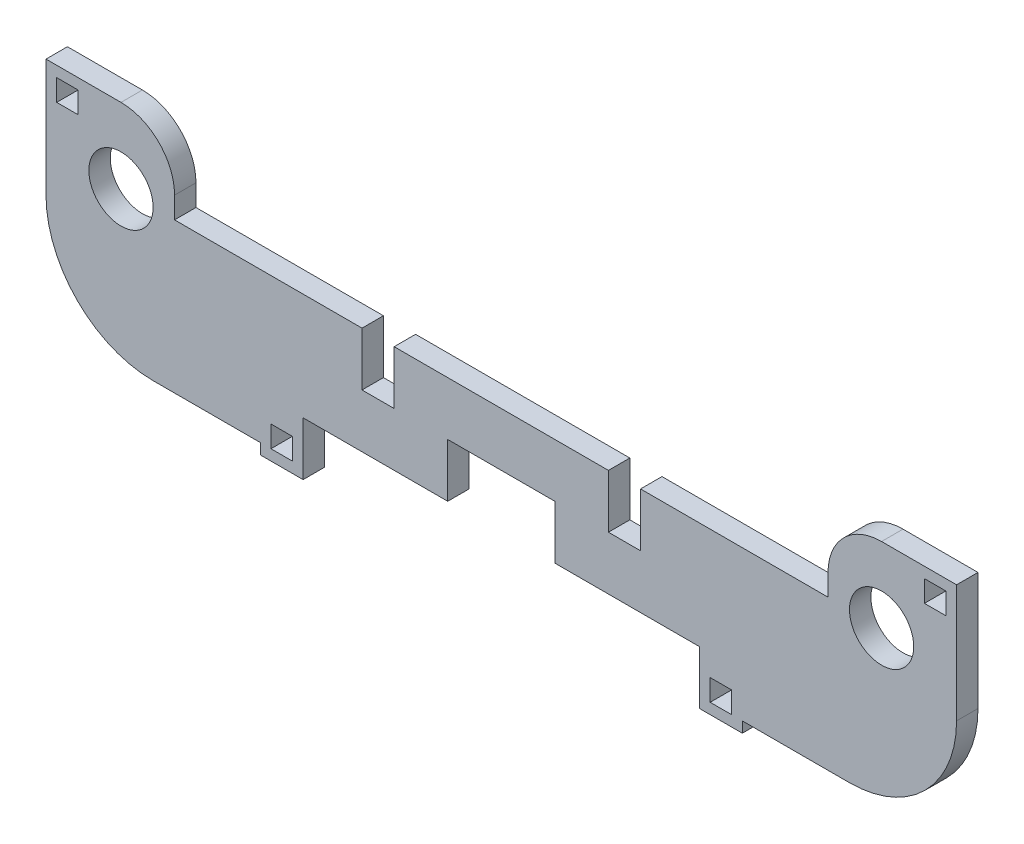
SolidWorks part; units mm, degrees
ref_plane "Front Plane" through (0, 0, 0) normal (0, 0, 1) x (1, 0, 0)
ref_plane "Top Plane" through (0, 0, 0) normal (0, 1, 0) x (1, 0, 0)
ref_plane "Right Plane" through (0, 0, 0) normal (1, 0, 0) x (0, 0, -1)
sketch "Sketch1" plane through (0, 0, 0) normal (0, 0, 1) x (1, 0, 0)
  line L0 (-35.5, -5) -> (35.5, 5) construction
  line L1 (-35.5, -5) -> (35.5, -5)
  line L2 (-35.5, -5) -> (-35.5, 5)
  line L3 (-35.5, 5) -> (-13, 5)
  line L4 (35.5, -5) -> (35.5, 5)
  line L5 (35.5, -5) -> (0, 0) construction
  line L6 (0, 0) -> (-35.5, 5) construction
  line L7 (-13, 5) -> (-13, 0)
  line L8 (-13, 0) -> (13, 0)
  line L9 (13, 0) -> (13, 5)
  line L10 (13, 5) -> (35.5, 5)
  line L11 (0, 0) -> (0, -5) construction
  line L12 (-35.5, 0) -> (-42.5, 0)
  line L13 (-42.5, 0) -> (-42.5, 12)
  line L14 (-42.5, 12) -> (-30.5, 12)
  line L15 (-30.5, 12) -> (-30.5, 5)
  line L16 (35.5, 0) -> (42.5, 0)
  line L17 (-41.5, 9) -> (-39.5, 9)
  line L18 (-41.5, 9) -> (-41.5, 11)
  line L19 (-41.5, 11) -> (-39.5, 11)
  line L20 (-39.5, 9) -> (-39.5, 11)
  line L21 (42.5, 0) -> (42.5, 12)
  line L22 (41.5, 11) -> (39.5, 11)
  line L23 (41.5, 9) -> (41.5, 11)
  line L24 (41.5, 9) -> (39.5, 9)
  line L25 (39.5, 9) -> (39.5, 11)
  line L26 (30.5, 12) -> (30.5, 5)
  line L27 (42.5, 12) -> (30.5, 12)
  line L28 (-5, -5) -> (-5, 0)
  line L29 (-5, 0) -> (5, 0)
  line L30 (5, 0) -> (5, -5)
  line L31 (0, 0) -> (0, -5) construction
  line L32 (-10, 0) -> (-10, 5)
  line L33 (-10, 5) -> (10, 5)
  line L34 (10, 5) -> (10, 0)
  line L35 (10, 0) -> (-10, 0)
  line L36 (0, 5) -> (0, 0) construction
  line L37 (18.5, -9) -> (18.5, -5)
  line L38 (-18.5, -9) -> (-18.5, -5)
  line L39 (-22.5, -9) -> (-22.5, -10)
  line L40 (21.5, -7) -> (19.5, -7)
  line L41 (21.5, -7) -> (21.5, -9)
  line L42 (21.5, -9) -> (19.5, -9)
  line L43 (19.5, -7) -> (19.5, -9)
  line L44 (-22.5, -10) -> (-18.5, -10)
  line L45 (-18.5, -10) -> (-18.5, -9)
  line L46 (-19.5, -7) -> (-19.5, -9)
  line L47 (42.5, -9) -> (22.5, -9)
  line L48 (22.5, -9) -> (22.5, -10)
  line L49 (22.5, -10) -> (18.5, -10)
  line L50 (18.5, -10) -> (18.5, -9)
  line L51 (35.5, -5) -> (42.5, -5)
  line L52 (42.5, -5) -> (42.5, 0)
  line L53 (-42.5, 0) -> (-42.5, -5)
  line L54 (-42.5, -5) -> (-35.5, -5)
  line L55 (-42.5, -5) -> (-42.5, -9)
  line L56 (-21.5, -7) -> (-19.5, -7)
  line L57 (42.5, -5) -> (42.5, -9)
  line L58 (-21.5, -7) -> (-21.5, -9)
  line L59 (-21.5, -9) -> (-19.5, -9)
  line L60 (-42.5, -9) -> (-22.5, -9)
  circle A0 centre (-35.5, 5) radius 3
  circle A1 centre (35.5, 5) radius 3
  dimension "D5" = 6
  dimension "D6" = 0
  dimension "D22" = 5
  dimension "D23" = 6
  dimension "D1" = 10
  dimension "D2" = 71
  dimension "D3" = 5
  dimension "D4" = 26
  dimension "D7" = 7
  dimension "D8" = 1
  dimension "D9" = 1
  dimension "D10" = 2
  dimension "D11" = 10
  dimension "D12" = 5
  dimension "D13" = 20
  dimension "D14" = 24
  dimension "D15" = 4
  dimension "D16" = 2
  dimension "D17" = 4
  dimension "D18" = 1
  dimension "D19" = 1
  dimension "D20" = 1
  dimension "D21" = 5
  dimension "D24" = 0
extrude "Boss-Extrude2" add sketch "Sketch1" along normal blind 2 contours A0 L3 L15 L14 L13 L12 L2 L20 L17 L18 L19 | L55 L60 L39 L44 L45 L38 L1 L54 L59 L58 L56 L46 | L53 L54 L2 L12 | A0 L2 L1 L28 L8 L7 L3 | L34 L33 L32 L8 | L57 L51 L1 L37 L50 L49 L48 L47 L43 L40 L41 L42 | L51 L52 L16 L4 | A1 L4 L16 L21 L27 L26 L10 L24 L25 L22 L23 | A1 L10 L9 L8 L30 L1 L4
fillet "Fillet1" radius 10 1 edges at (-42.5, -9, 1)
fillet "Fillet2" radius 10 1 edges at (42.5, -9, 1)
fillet "Fillet3" radius 5 1 edges at (-30.5, 12, 1)
fillet "Fillet4" radius 5 1 edges at (30.5, 12, 1)
